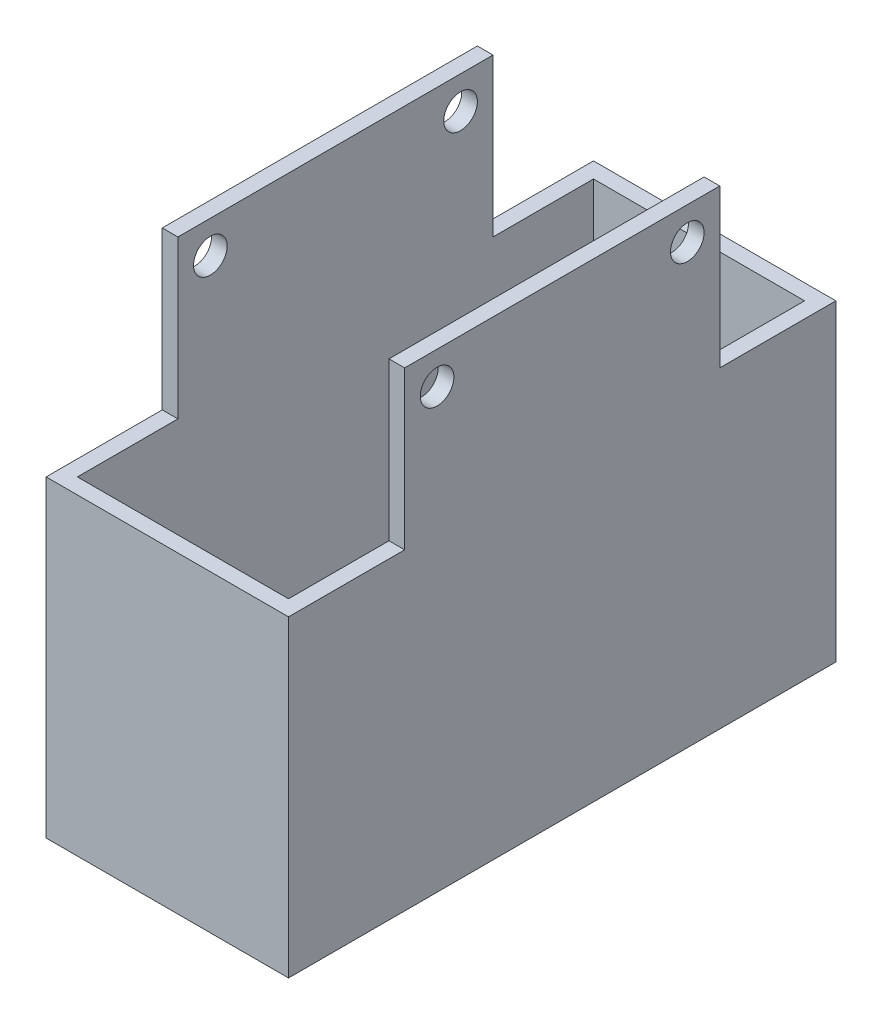
SolidWorks part; units mm, degrees
material "ABS"
ref_plane "Alzado" through (0, 0, 0) normal (0, 0, 1) x (1, 0, 0)
ref_plane "Planta" through (0, 0, 0) normal (0, 1, 0) x (1, 0, 0)
ref_plane "Vista lateral" through (0, 0, 0) normal (1, 0, 0) x (0, 0, -1)
sketch "Croquis1" plane through (0, 0, 0) normal (0, 1, 0) x (1, 0, 0)
  line L1 (15.5, -35) -> (-15.5, -35)
  line L2 (15.5, -35) -> (15.5, 35)
  line L3 (15.5, 35) -> (-15.5, 35)
  line L4 (-15.5, -35) -> (-15.5, 35)
  line L5 (15.5, -35) -> (-15.5, 35) construction
  line L6 (15.5, 35) -> (-15.5, -35) construction
  line L7 (13.5, -33) -> (-13.5, -33)
  line L8 (13.5, -33) -> (13.5, 33)
  line L9 (13.5, 33) -> (-13.5, 33)
  line L10 (-13.5, -33) -> (-13.5, 33)
  line L11 (13.5, -33) -> (-13.5, 33) construction
  line L12 (13.5, 33) -> (-13.5, -33) construction
  point P0 (0, 0)
  point P6 (0, 0)
  dimension "D1" = 70
  dimension "D2" = 31
  dimension "D3" = 2
  dimension "D4" = 2
extrude "Saliente-Extruir1" add sketch "Croquis1" along normal blind 40
sketch "Croquis4" plane through (15.5, 0, 0) normal (1, 0, 0) x (0, 0, -1)
  line L0 (0, 0) -> (0, 40) construction
  line L1 (-35, 40) -> (35, 40) construction
  line L2 (0, 40) -> (0, 56) construction
  line L3 (0, 56) -> (-16, 56) construction
  line L4 (0, 56) -> (16, 56) construction
  line L5 (-20.15, 40) -> (-20.15, 60.15)
  line L6 (-20.15, 60.15) -> (20.15, 60.15)
  line L7 (20.15, 60.15) -> (20.15, 40)
  circle A0 centre (-16, 56) radius 2.15
  circle A1 centre (16, 56) radius 2.15
  line M10 (35, 40) -> (-35, 40)
  dimension "D3" = 4.3
  dimension "D4" = 2
  dimension "D5" = 2
  dimension "D1" = 32
  dimension "D2" = 16
extrude "Saliente-Extruir2" add sketch "Croquis4" against normal through all contours L7 L6 L5 A1 A0 M10
sketch "Croquis5" plane through (0, 60.15, 0) normal (0, 1, 0) x (1, 0, 0)
  line L1 (-13.5, 20.15) -> (13.5, 20.15)
  line L2 (-13.5, 20.15) -> (-13.5, -20.15)
  line L3 (-13.5, -20.15) -> (13.5, -20.15)
  line L4 (13.5, 20.15) -> (13.5, -20.15)
extrude "Cortar-Extruir2" cut sketch "Croquis5" against normal blind 40
sketch "Croquis6" plane through (0, 0, 0) normal (0, -1, 0) x (1, 0, 0)
  line L1 (-15.5, 35) -> (15.5, 35)
  line L2 (-15.5, 35) -> (-15.5, -35)
  line L3 (-15.5, -35) -> (15.5, -35)
  line L4 (15.5, 35) -> (15.5, -35)
extrude "Saliente-Extruir3" add sketch "Croquis6" against normal blind 3
